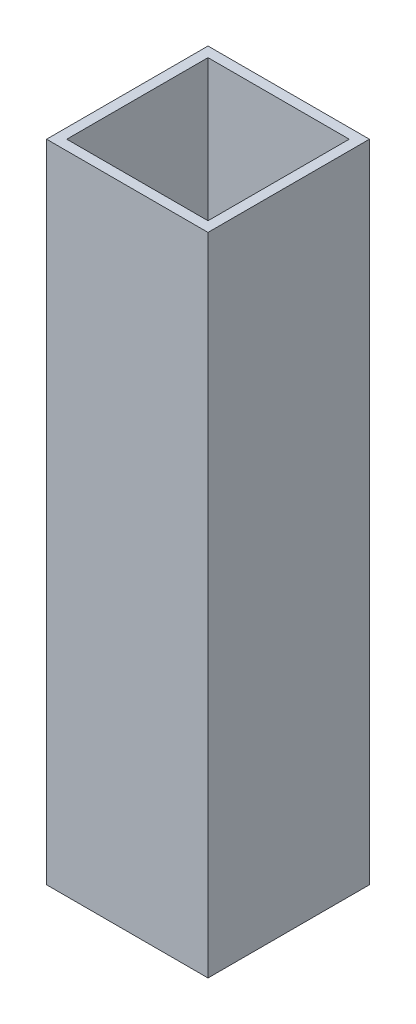
SolidWorks part; units mm, degrees
material "6061-T6 (SS)"
ref_plane "Front Plane" through (0, 0, 0) normal (0, 0, 1) x (1, 0, 0)
ref_plane "Top Plane" through (0, 0, 0) normal (0, 1, 0) x (1, 0, 0)
ref_plane "Right Plane" through (0, 0, 0) normal (1, 0, 0) x (0, 0, -1)
sketch "Sketch1" plane through (0, 0, 0) normal (0, 1, 0) x (1, 0, 0)
  line L0 (-11.1125, -11.1125) -> (11.1125, -11.1125)
  line L1 (-12.7, 12.7) -> (12.7, 12.7)
  line L2 (-12.7, 12.7) -> (-12.7, -12.7)
  line L3 (-12.7, -12.7) -> (12.7, -12.7)
  line L4 (12.7, 12.7) -> (12.7, -12.7)
  line L5 (-12.7, 12.7) -> (12.7, -12.7) construction
  line L6 (-12.7, -12.7) -> (12.7, 12.7) construction
  line L7 (11.1125, 11.1125) -> (11.1125, -11.1125)
  line L8 (-11.1125, 11.1125) -> (11.1125, 11.1125)
  line L9 (-11.1125, 11.1125) -> (-11.1125, -11.1125)
  point P0 (0, 0)
  dimension "D1" = 25.4
  dimension "D2" = 25.4
  dimension "D3" = 1.5875
extrude "Boss-Extrude1" add sketch "Sketch1" along normal blind 101.6
